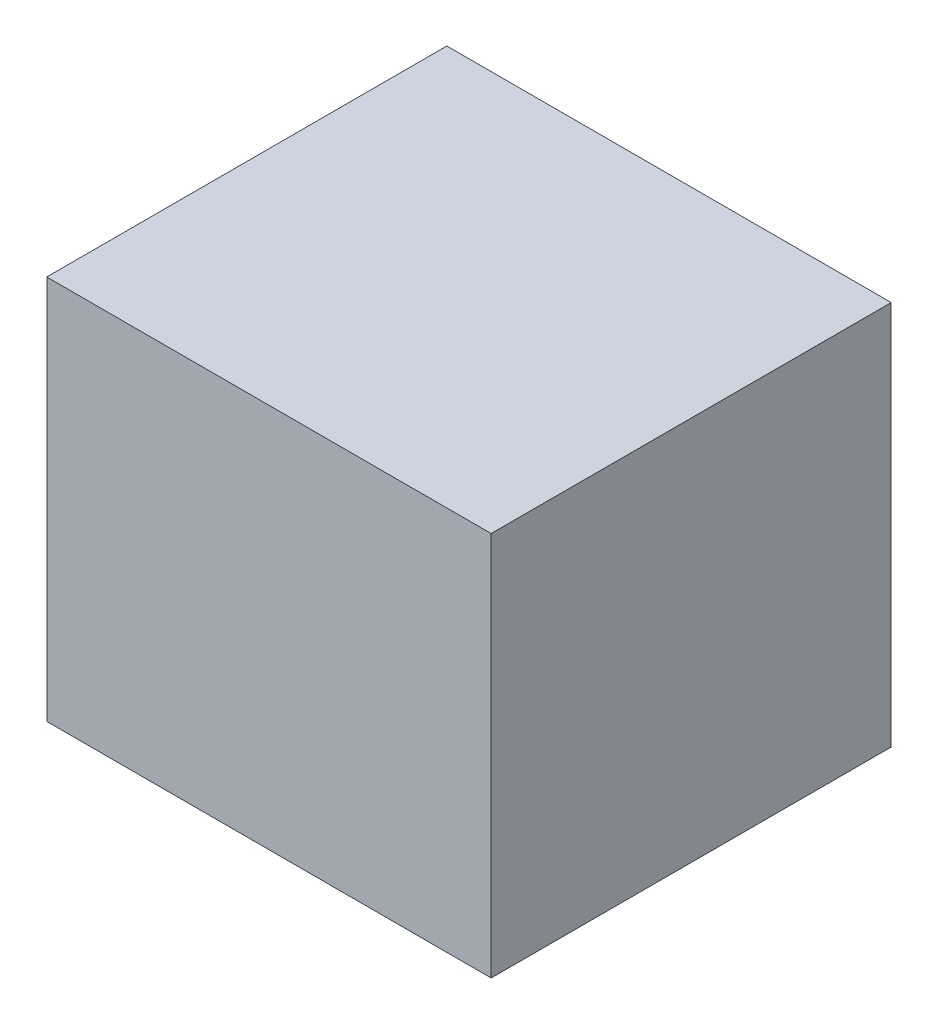
SolidWorks part; units mm, degrees
ref_plane "Front Plane" through (0, 0, 0) normal (0, 0, 1) x (1, 0, 0)
ref_plane "Top Plane" through (0, 0, 0) normal (0, 1, 0) x (1, 0, 0)
ref_plane "Right Plane" through (0, 0, 0) normal (1, 0, 0) x (0, 0, -1)
sketch "Sketch1" plane through (0, 0, 0) normal (0, 1, 0) x (1, 0, 0)
  line L1 (-3.81, -3.43) -> (3.81, -3.43)
  line L2 (-3.81, -3.43) -> (-3.81, 3.43)
  line L3 (-3.81, 3.43) -> (3.81, 3.43)
  line L4 (3.81, -3.43) -> (3.81, 3.43)
  line L5 (-3.81, -3.43) -> (3.81, 3.43) construction
  line L6 (-3.81, 3.43) -> (3.81, -3.43) construction
  point P0 (0, 0)
  dimension "D1" = 7.62
  dimension "D2" = 6.86
extrude "Boss-Extrude1" add sketch "Sketch1" along normal blind 6.6
